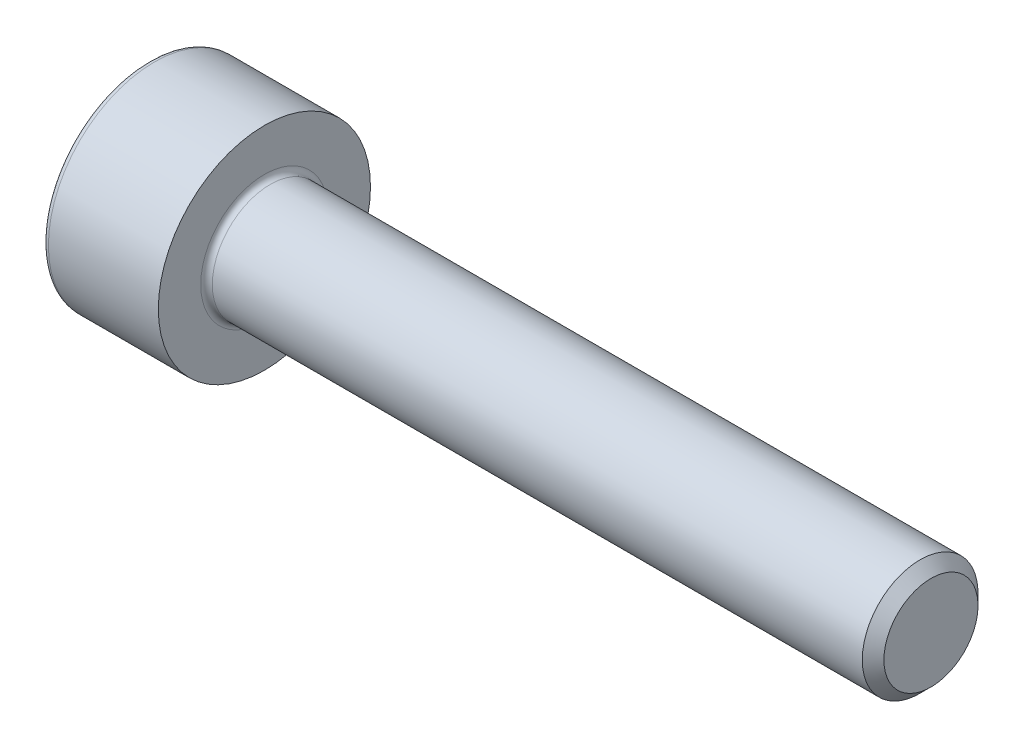
SolidWorks part; units mm, degrees
ref_plane "Front Plane" through (0, 0, 0) normal (0, 0, 1) x (1, 0, 0)
ref_plane "Top Plane" through (0, 0, 0) normal (0, 1, 0) x (1, 0, 0)
ref_plane "Right Plane" through (0, 0, 0) normal (1, 0, 0) x (0, 0, -1)
sketch "Sketch1" plane through (0, 0, 0) normal (0, 1, 0) x (1, 0, 0)
  line L0 (-11.4492, 2.2988) -> (-11.4492, -0.4512)
  line L1 (-11.4492, 2.2988) -> (-8.4492, 2.2988)
  line L2 (-8.4492, 2.2988) -> (-8.4492, 1.0488)
  line L3 (-8.4492, 1.0488) -> (8.5508, 1.0488)
  line L4 (8.5508, 1.0488) -> (8.8313, 0.7683)
  line L5 (8.8313, 0.7683) -> (8.8313, -0.4512)
  line L6 (8.8313, -0.4512) -> (-11.4492, -0.4512)
  line L7 (-15.5125, -0.4512) -> (-0.0951, -0.4512) construction
  dimension "D1" = 2.75
  dimension "D2" = 1.25
  dimension "D3" = 135
  dimension "D4" = 135
  dimension "D5" = 3
  dimension "D6" = 17
  dimension "D8" = 1.2195
revolve "Revolve2" add sketch "Sketch1" angle 360 about L7
fillet "Fillet2" radius 0.15 2 edges at (-11.4492, 0, 3.2012) (-8.4492, 0, 1.9512)
sketch "Sketch3" plane through (-11.4492, 0, 0) normal (-1, 0, 0) x (0, 0, 1)
  line L0 (0.4512, 2.6) -> (0.4512, -2.6) construction
  line L2 (3.0512, 0) -> (-2.1488, 0) construction
  line L5 (1.1901, -1.28) -> (1.9292, -0.0001)
  line L6 (1.9292, -0.0001) -> (1.1902, 1.28)
  line L7 (1.1902, 1.28) -> (-0.2878, 1.28)
  line L8 (-0.2878, 1.28) -> (-1.0268, 0.0001)
  line L9 (-1.0268, 0.0001) -> (-0.2879, -1.28)
  line L10 (-0.2879, -1.28) -> (1.1901, -1.28)
  circle A0 centre (0.4512, 0) radius 2.6 construction
  circle A1 centre (0.4512, 0) radius 1.28 construction
  dimension "D3" = 1.478
extrude "Cut-Extrude1" cut sketch "Sketch3" against normal blind 1
